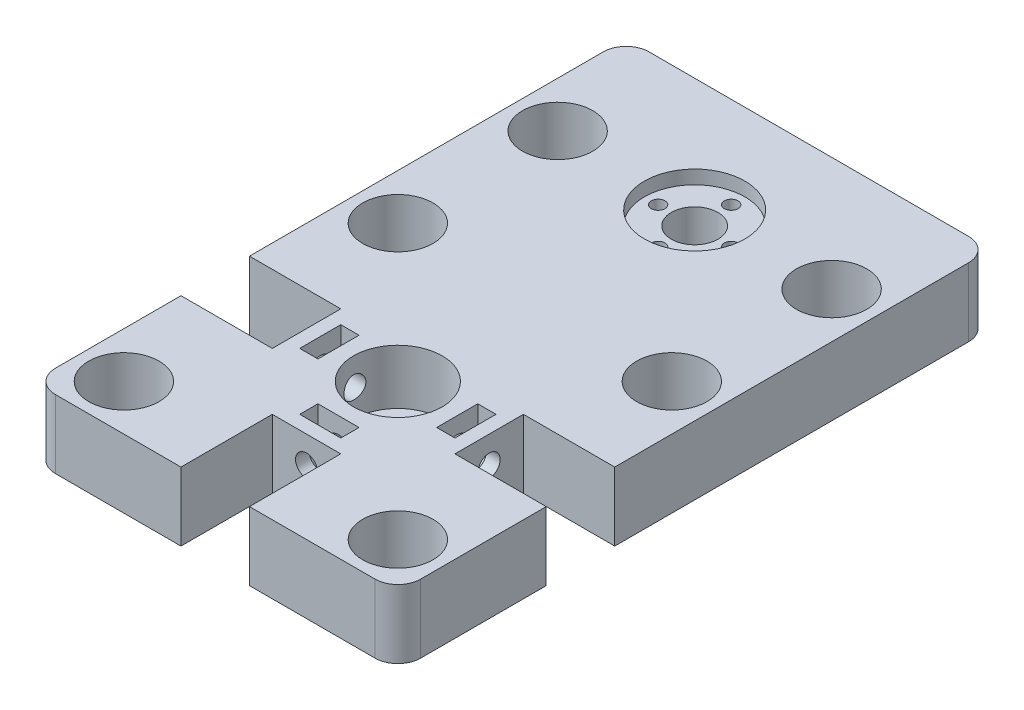
SolidWorks part; units mm, degrees
material "ABS"
ref_plane "Plano frontal" through (0, 0, 0) normal (0, 0, 1) x (1, 0, 0)
ref_plane "Plano superior" through (0, 0, 0) normal (0, 1, 0) x (1, 0, 0)
ref_plane "Plano direito" through (0, 0, 0) normal (1, 0, 0) x (0, 0, -1)
sketch "Esboço1" plane through (0, 0, 0) normal (0, 1, 0) x (1, 0, 0)
  line L1 (40, -65) -> (-40, -65)
  line L2 (40, -65) -> (40, 65)
  line L3 (40, 65) -> (-40, 65)
  line L4 (-40, -65) -> (-40, 65)
  line L5 (40, -65) -> (-40, 65) construction
  line L6 (40, 65) -> (-40, -65) construction
  point P0 (0, 0)
  dimension "D1" = 80
  dimension "D2" = 130
extrude "Ressalto-extrusão1" add sketch "Esboço1" along normal blind 15
sketch "Esboço2" plane through (0, 15, 0) normal (0, 1, 0) x (1, 0, 0)
  line L0 (0, -66.4073) -> (0, 73.9427) construction
  line L1 (-40, 15) -> (40, 15) construction
  line L2 (-40, 65) -> (-40, -65) construction
  line L3 (40, -65) -> (40, 65) construction
  line L4 (-40, -65) -> (40, -65) construction
  line L5 (-40, -25) -> (40, -25) construction
  line L6 (-40, 40) -> (40, 40) construction
  line L7 (40, 65) -> (-40, 65) construction
  circle A0 centre (-30, 5) radius 7.7
  circle A1 centre (30, 5) radius 7.7
  circle A2 centre (-30, -55) radius 7.7
  circle A3 centre (30, -55) radius 7.7
  circle A4 centre (-30, 40) radius 7.7
  circle A5 centre (30, 40) radius 7.7
  dimension "D3" = 15.4
  dimension "D4" = 10
  dimension "D5" = 10
  dimension "D7" = 10
  dimension "D1" = 80
  dimension "D2" = 40
  dimension "D6" = 25
extrude "Corte-extrusão1" cut sketch "Esboço2" against normal through all
sketch "Esboço3" plane through (0, 15, 0) normal (0, 1, 0) x (1, 0, 0)
  line L0 (0, -75.2175) -> (0, 94.9461) construction
  line L1 (-40, 15) -> (40, 15) construction
  line L2 (-40, 65) -> (-40, -65) construction
  line L3 (40, -65) -> (40, 65) construction
  line L4 (-40, -65) -> (40, -65) construction
  line L5 (-40, -25) -> (40, -25) construction
  circle A0 centre (0, -25) radius 9.7
  dimension "D3" = 19.4
  dimension "D1" = 80
  dimension "D2" = 40
extrude "Corte-extrusão2" cut sketch "Esboço3" against normal blind 12
sketch "Esboço4" plane through (0, 3, 0) normal (0, 1, 0) x (1, 0, 0)
  line L0 (0, 76.5007) -> (0, -80.7599) construction
  circle A0 centre (0, -25) radius 4.6
  circle A1 centre (0, -25) radius 9.7 construction
  dimension "D1" = 9.2
extrude "Corte-extrusão3" cut sketch "Esboço4" against normal through all
sketch "Esboço5" plane through (0, 15, 0) normal (0, 1, 0) x (1, 0, 0)
  line L0 (0, -75.7636) -> (0, 69.2111) construction
  line L1 (-40, -65) -> (40, -65) construction
  line L2 (7.5, -45) -> (-7.5, -45)
  line L3 (7.5, -45) -> (7.5, -65)
  line L4 (7.5, -65) -> (-7.5, -65)
  line L5 (-7.5, -45) -> (-7.5, -65)
  line L6 (7.5, -45) -> (-7.5, -65) construction
  line L7 (7.5, -65) -> (-7.5, -45) construction
  line L8 (0, -25) -> (77.7829, -25) construction
  line L9 (40, -65) -> (40, 65) construction
  line L10 (20, -32.5) -> (40, -32.5)
  line L11 (20, -32.5) -> (20, -17.5)
  line L12 (20, -17.5) -> (40, -17.5)
  line L13 (40, -32.5) -> (40, -17.5)
  line L14 (20, -32.5) -> (40, -17.5) construction
  line L15 (20, -17.5) -> (40, -32.5) construction
  line L16 (-20, -17.5) -> (-40, -17.5)
  line L17 (-40, -32.5) -> (-40, -17.5)
  line L18 (-20, -32.5) -> (-40, -32.5)
  line L19 (-20, -32.5) -> (-20, -17.5)
  point P3 (0, -55)
  point P13 (30, -25)
  dimension "D1" = 20
  dimension "D2" = 15
  dimension "D3" = 20
  dimension "D4" = 15
extrude "Corte-extrusão4" cut sketch "Esboço5" against normal through all
sketch "Esboço6" plane through (0, 0, 45) normal (0, 0, 1) x (1, 0, 0)
  line L0 (0, -6.1969) -> (0, 21.4566) construction
  line L1 (7.5, 15) -> (-7.5, 15) construction
  circle A0 centre (0, 9) radius 2.4
  dimension "D1" = 4.8
  dimension "D2" = 6
extrude "Corte-extrusão5" cut sketch "Esboço6" against normal blind 15
sketch "Esboço7" plane through (20, 0, 0) normal (1, 0, 0) x (0, 0, -1)
  line L0 (-25, 18.2886) -> (-25, -3.7869) construction
  line L1 (-17.5, 15) -> (-32.5, 15) construction
  circle A0 centre (-25, 9) radius 2.4
  dimension "D1" = 4.8
  dimension "D2" = 6
extrude "Corte-extrusão6" cut sketch "Esboço7" against normal blind 15
sketch "Esboço8" plane through (0, 15, 0) normal (0, 1, 0) x (1, 0, 0)
  line L0 (-40, 15) -> (40, 15) construction
  line L1 (-40, 65) -> (-40, -17.5) construction
  line L2 (40, -17.5) -> (40, 65) construction
  line L3 (40, 65) -> (-40, 65) construction
  line L4 (0, -74.3985) -> (0, 87.8694) construction
  line L5 (-40, 40) -> (40, 40) construction
  circle A0 centre (0, 40) radius 11
  dimension "D3" = 22
  dimension "D1" = 50
  dimension "D2" = 25
extrude "Corte-extrusão7" cut sketch "Esboço8" against normal blind 3
sketch "Esboço10" plane through (0, 12, 0) normal (0, 1, 0) x (1, 0, 0)
  line L0 (0, 55.5468) -> (0, 18.9741) construction
  line L1 (-13.8913, 40) -> (14.2605, 40) construction
  circle A0 centre (0, 40) radius 5.1
  circle A1 centre (0, 48) radius 1.5
  circle A2 centre (8, 40) radius 1.5
  circle A3 centre (0, 32) radius 1.5
  circle A4 centre (-8, 40) radius 1.5
  dimension "D1" = 10.2
  dimension "D2" = 3
  dimension "D3" = 8
  dimension "D4" = 4
extrude "Corte-extrusão9" cut sketch "Esboço10" against normal through all
fillet "Filete1" radius 5 2 edges at (40, 7.5, -65) (-40, 7.5, -65)
fillet "Filete2" radius 5 2 edges at (40, 7.5, 65) (-40, 7.5, 65)
sketch "Esboço11" plane through (-20, 0, 0) normal (-1, 0, 0) x (0, 0, 1)
  line L0 (25, 17.8038) -> (25, -4.0235) construction
  line L1 (32.5, 15) -> (17.5, 15) construction
  circle A0 centre (25, 9) radius 2.4
  dimension "D1" = 4.8
  dimension "D2" = 6
extrude "Corte-extrusão10" cut sketch "Esboço11" against normal blind 15
ref_plane "Plano1" through (-17, 0, 0) normal (-1, 0, 0) x (0, 0, 1)
sketch "Esboço12" plane through (-17, 0, 0) normal (-1, 0, 0) x (0, 0, 1)
  line L0 (25, 17.7262) -> (25, -2.8488) construction
  line L1 (32.5, 15) -> (17.5, 15) construction
  line L2 (14.7944, 9) -> (35.5403, 9) construction
  line L3 (22.75, 5.1029) -> (27.25, 5.1029)
  line L4 (20.5, 9) -> (22.75, 5.1029)
  line L5 (29.5, 9) -> (27.25, 5.1029)
  line L6 (20.5, 9) -> (20.5, 15)
  line L7 (29.5, 9) -> (29.5, 15)
  line L8 (20.5, 15) -> (29.5, 15)
  circle A0 centre (25, 9) radius 4.5 construction
  point P4 (25, 15)
  point P11 (25, 5.1029)
  dimension "D2" = 9
  dimension "D1" = 6
extrude "Corte-extrusão11" cut sketch "Esboço12" against normal blind 4
ref_plane "Plano2" through (0, 0, 42) normal (0, 0, 1) x (1, 0, 0)
sketch "Esboço13" plane through (0, 0, 42) normal (0, 0, 1) x (1, 0, 0)
  line L0 (0, 19.6028) -> (0, -2.3385) construction
  line L1 (7.5, 15) -> (-7.5, 15) construction
  line L2 (-9.7078, 9) -> (10.4324, 9) construction
  line L3 (-2.25, 5.1029) -> (2.25, 5.1029)
  line L4 (-4.5, 9) -> (-2.25, 5.1029)
  line L5 (4.5, 9) -> (2.25, 5.1029)
  line L6 (-4.5, 9) -> (-4.5, 15)
  line L7 (4.5, 9) -> (4.5, 15)
  line L8 (-4.5, 15) -> (4.5, 15)
  circle A0 centre (0, 9) radius 4.5 construction
  point P4 (0, 15)
  point P11 (0, 5.1029)
  dimension "D2" = 9
  dimension "D1" = 6
extrude "Corte-extrusão12" cut sketch "Esboço13" against normal blind 4
ref_plane "Plano3" through (17, 0, 0) normal (1, 0, 0) x (0, 0, -1)
sketch "Esboço14" plane through (17, 0, 0) normal (1, 0, 0) x (0, 0, -1)
  line L0 (-25, 17.5812) -> (-25, -2.8124) construction
  line L1 (-17.5, 15) -> (-32.5, 15) construction
  line L2 (-35.3015, 9) -> (-11.9926, 9) construction
  line L3 (-27.25, 5.1029) -> (-22.75, 5.1029)
  line L4 (-29.5, 9) -> (-27.25, 5.1029)
  line L5 (-20.5, 9) -> (-22.75, 5.1029)
  line L6 (-29.5, 15) -> (-29.5, 9)
  line L7 (-20.5, 15) -> (-20.5, 9)
  line L8 (-29.5, 15) -> (-20.5, 15)
  circle A0 centre (-25, 9) radius 4.5 construction
  point P4 (-25, 15)
  point P11 (-25, 5.1029)
  dimension "D2" = 9
  dimension "D1" = 6
extrude "Corte-extrusão13" cut sketch "Esboço14" against normal blind 4
